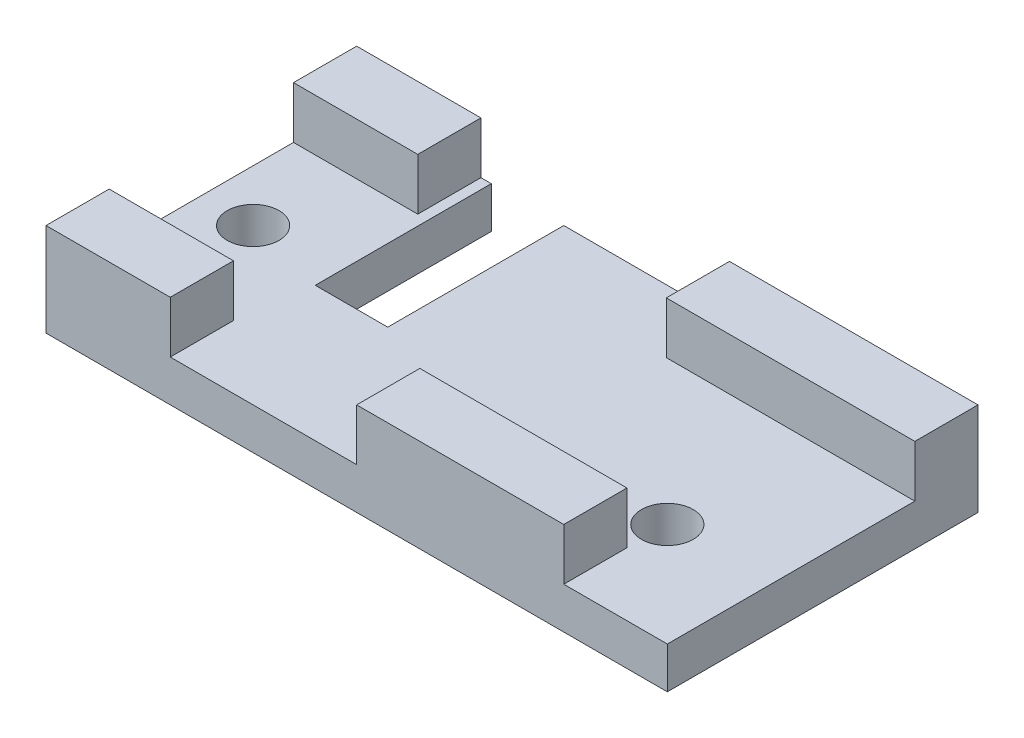
SolidWorks part; units mm, degrees
ref_plane "Front Plane" through (0, 0, 0) normal (0, 0, 1) x (1, 0, 0)
ref_plane "Top Plane" through (0, 0, 0) normal (0, 1, 0) x (1, 0, 0)
ref_plane "Right Plane" through (0, 0, 0) normal (1, 0, 0) x (0, 0, -1)
sketch "Sketch1" plane through (0, 0, 0) normal (0, 1, 0) x (1, 0, 0)
  line L1 (-38.1, -19.05) -> (38.1, -19.05)
  line L2 (-38.1, -19.05) -> (-38.1, 19.05)
  line L3 (-38.1, 19.05) -> (38.1, 19.05)
  line L4 (38.1, -19.05) -> (38.1, 19.05)
  line L5 (-38.1, -19.05) -> (38.1, 19.05) construction
  line L6 (-38.1, 19.05) -> (38.1, -19.05) construction
  point P0 (0, 0)
  dimension "D1" = 38.1
  dimension "D2" = 76.2
extrude "Boss-Extrude1" add sketch "Sketch1" along normal mid plane 5.08
sketch "Sketch2" plane through (0, 2.54, 0) normal (0, 1, 0) x (1, 0, 0)
  line L0 (0, -19.05) -> (0, -11.303) construction
  line L1 (0, -11.303) -> (38.1, -11.303) construction
  line L2 (38.1, -11.303) -> (38.1, -19.05) construction
  line L3 (38.1, -19.05) -> (0, -19.05) construction
  line L4 (0, 11.303) -> (0, 19.05) construction
  line L5 (0, 19.05) -> (38.1, 19.05) construction
  line L6 (38.1, 19.05) -> (38.1, 11.303) construction
  line L7 (38.1, 11.303) -> (0, 11.303) construction
  line L8 (-38.1, -19.05) -> (-38.1, -11.303) construction
  line L9 (-38.1, -11.303) -> (-22.86, -11.303) construction
  line L10 (-22.86, -11.303) -> (-22.86, -19.05) construction
  line L11 (-22.86, -19.05) -> (-38.1, -19.05) construction
  line L12 (-38.1, 11.303) -> (-38.1, 19.05) construction
  line L13 (-38.1, 19.05) -> (-22.86, 19.05) construction
  line L14 (-22.86, 19.05) -> (-22.86, 11.303) construction
  line L15 (-22.86, 11.303) -> (-38.1, 11.303) construction
  line L16 (0, -19.05) -> (0, -11.303)
  line L17 (0, -11.303) -> (38.1, -11.303)
  line L18 (38.1, -11.303) -> (38.1, -19.05)
  line L19 (38.1, -19.05) -> (0, -19.05)
  line L20 (0, 11.303) -> (0, 19.05)
  line L21 (0, 19.05) -> (38.1, 19.05)
  line L22 (38.1, 19.05) -> (38.1, 11.303)
  line L23 (38.1, 11.303) -> (0, 11.303)
  line L24 (-38.1, -19.05) -> (-38.1, -11.303)
  line L25 (-38.1, -11.303) -> (-22.86, -11.303)
  line L26 (-22.86, -11.303) -> (-22.86, -19.05)
  line L27 (-22.86, -19.05) -> (-38.1, -19.05)
  line L28 (-38.1, 11.303) -> (-38.1, 19.05)
  line L29 (-38.1, 19.05) -> (-22.86, 19.05)
  line L30 (-22.86, 19.05) -> (-22.86, 11.303)
  line L31 (-22.86, 11.303) -> (-38.1, 11.303)
  line L32 (7.62, 11.303) -> (7.62, 19.05)
  line M1 (38.1, -19.05) -> (38.1, 19.05)
  line M2 (38.1, 19.05) -> (-38.1, 19.05)
  line M3 (-38.1, 19.05) -> (-38.1, -19.05)
  line M4 (-38.1, -19.05) -> (38.1, -19.05)
  dimension "D1" = 7.62
extrude "Boss-Extrude2" add sketch "Sketch2" along normal up to surface (6.35 mm away) contours L31 L30 M2 M3 | L32 L23 M1 M2 | L17 L16 M4 M1 | L26 L25 M3 M4
sketch "Sketch3" plane through (0, 2.54, 0) normal (0, 1, 0) x (1, 0, 0)
  line L0 (7.62, 19.05) -> (-22.86, 19.05) construction
  line L1 (-12.7, 19.05) -> (-21.59, 19.05)
  line L2 (-12.7, 19.05) -> (-12.7, -2.54)
  line L3 (-12.7, -2.54) -> (-21.59, -2.54)
  line L4 (-21.59, 19.05) -> (-21.59, -2.54)
  line L7 (7.62, 19.05) -> (7.62, 11.303) construction
  dimension "D1" = 20.32
  dimension "D2" = 21.59
  dimension "D3" = 8.89
extrude "Cut-Extrude1" cut sketch "Sketch3" against normal through all
sketch "Sketch4" plane through (0, 0, 19.05) normal (0, 0, 1) x (1, 0, 0)
  line L0 (-22.86, 2.54) -> (0, 2.54) construction
  line L1 (38.1, 8.89) -> (25.4, 8.89)
  line L2 (38.1, 8.89) -> (38.1, 2.54)
  line L3 (38.1, 2.54) -> (25.4, 2.54)
  line L4 (25.4, 8.89) -> (25.4, 2.54)
  dimension "D1" = 12.7
extrude "Cut-Extrude2" cut sketch "Sketch4" against normal up to surface (7.747 mm away) up to face at (19.05, 5.715, 11.303)
sketch "Sketch5" plane through (0, -2.54, 0) normal (0, -1, 0) x (1, 0, 0)
  circle A0 centre (25.4, 6.35) radius 3.175 construction
  circle A1 centre (-31.75, 0) radius 3.175 construction
  circle A2 centre (25.4, 6.35) radius 3.175
  circle A3 centre (-31.75, 0) radius 3.175
extrude "Cut-Extrude3" cut sketch "Sketch5" against normal through all
